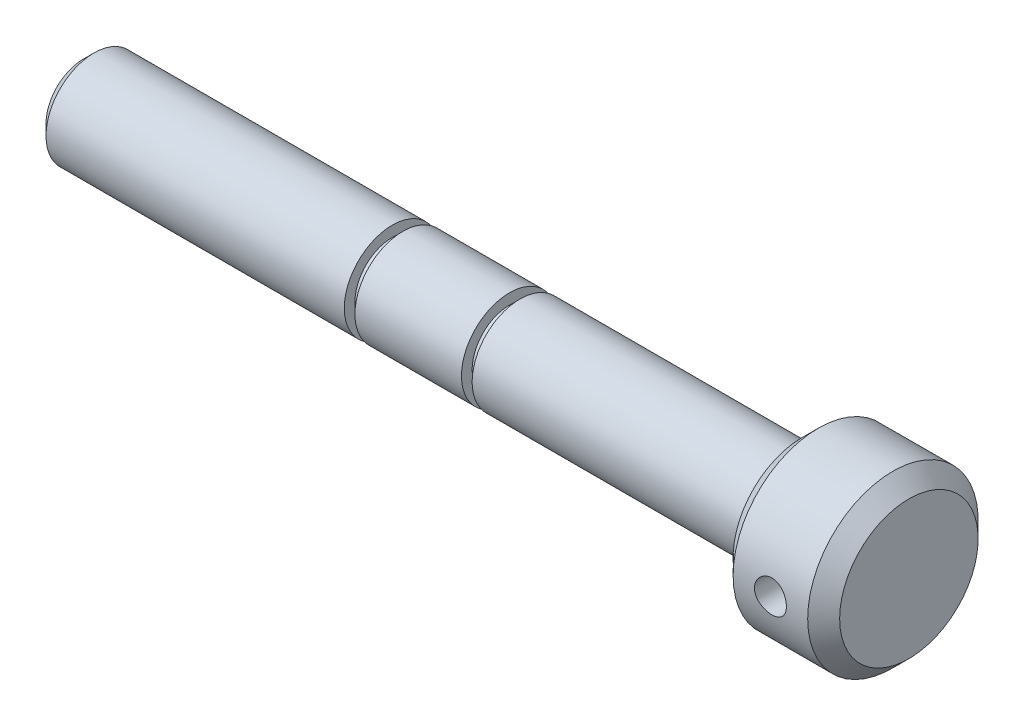
SolidWorks part; units mm, degrees
ref_plane "Front Plane" through (0, 0, 0) normal (0, 0, 1) x (1, 0, 0)
ref_plane "Top Plane" through (0, 0, 0) normal (0, 1, 0) x (1, 0, 0)
ref_plane "Right Plane" through (0, 0, 0) normal (1, 0, 0) x (0, 0, -1)
sketch "Sketch1" plane through (0, 0, 0) normal (0, 0, 1) x (1, 0, 0)
  line L0 (0, 0) -> (155, 0) construction
  line L1 (155, 0) -> (155, 16)
  line L2 (155, 16) -> (135, 16)
  line L3 (135, 16) -> (135, 9)
  line L4 (135, 9) -> (82, 9)
  line L5 (82, 9) -> (82, 7)
  line L6 (82, 7) -> (80, 7)
  line L7 (80, 7) -> (80, 9)
  line L8 (80, 9) -> (60, 9)
  line L9 (60, 9) -> (60, 7)
  line L10 (60, 7) -> (58, 7)
  line L11 (58, 7) -> (58, 9)
  line L12 (58, 9) -> (0, 9)
  line L13 (0, 9) -> (0, 0)
  line L14 (0, 0) -> (155, 0)
  dimension "D1" = 155
  dimension "D2" = 16
  dimension "D3" = 20
  dimension "D4" = 53
  dimension "D5" = 7
  dimension "D6" = 2
  dimension "D7" = 20
  dimension "D8" = 9
revolve "Revolve1" add sketch "Sketch1" angle 360 about L0
cosmetic thread "Cosmetic Thread2" parameters "D2"=15.252
chamfer "Chamfer1" distance 3 angle 45 2 edges at (135, 0, 16) (155, 0, 16)
chamfer "Chamfer2" distance 2 angle 45 1 edges at (0, 0, 9)
cosmetic thread "Cosmetic Thread1" parameters "D2"=15.252
sketch "Sketch2" plane through (0, 0, 0) normal (0, 0, 1) x (1, 0, 0)
  line L0 (155, -13) -> (155, 13) construction
  circle A0 centre (145, 0) radius 3
  dimension "D1" = 6
  dimension "D2" = 10
extrude "Cut-Extrude1" cut sketch "Sketch2" against normal through all both and the other way through all
